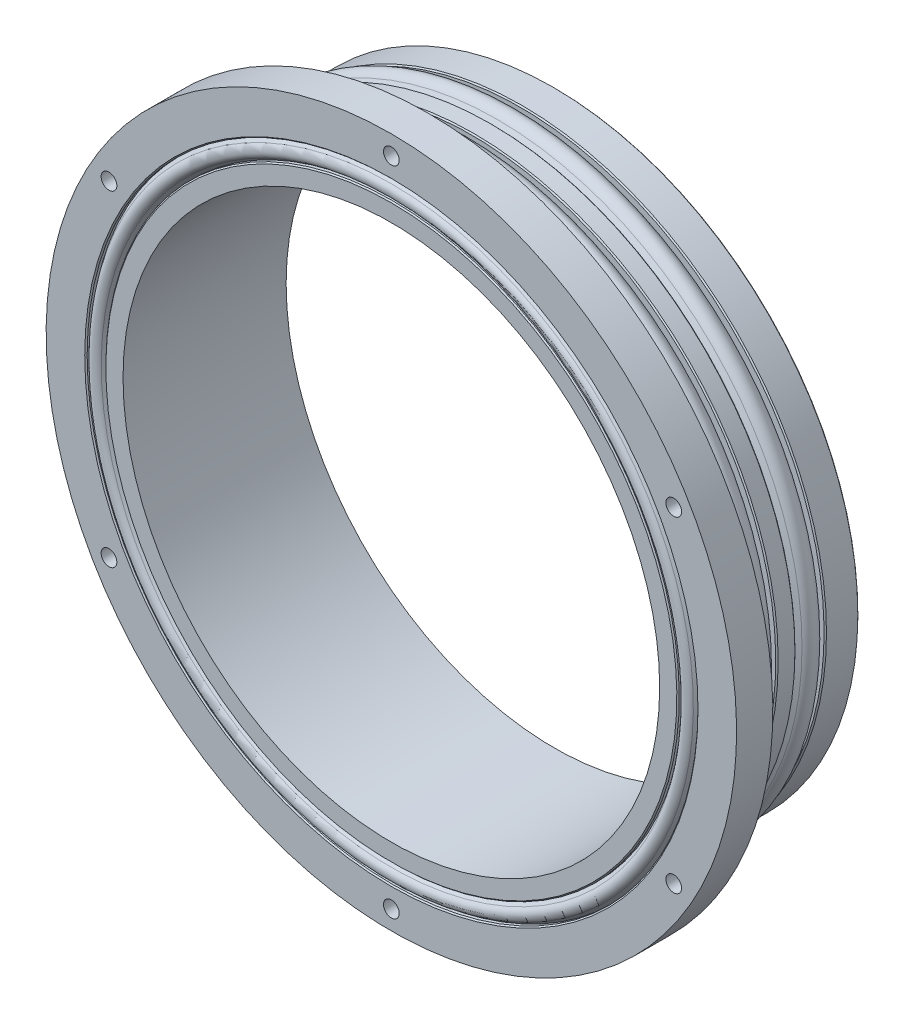
SolidWorks part; units mm, degrees
ref_plane "前视基准面" through (0, 0, 0) normal (0, 0, 1) x (1, 0, 0)
ref_plane "上视基准面" through (0, 0, 0) normal (0, 1, 0) x (1, 0, 0)
ref_plane "右视基准面" through (0, 0, 0) normal (1, 0, 0) x (0, 0, -1)
ref_plane "基准面4" through (0, 0, 0) normal (0, -1, 0) x (1, 0, 0)
sketch "草图1" plane through (0, 0, 0) normal (0, -1, 0) x (1, 0, 0)
  line L0 (47.2599, 27) -> (0, 27)
  line L1 (0, 27) -> (0, 0)
  line L2 (0, 0) -> (50.419, 0)
  line L3 (50.419, 0) -> (50.419, 5.587)
  line L4 (50.419, 5.587) -> (49.0411, 5.587)
  line L5 (49.0411, 5.587) -> (50.4317, 6.5475)
  line L6 (50.4317, 9.4525) -> (49.0411, 10.413)
  line L7 (49.0411, 10.413) -> (50.419, 10.413)
  line L8 (50.419, 10.413) -> (50.419, 13.587)
  line L9 (50.419, 13.587) -> (49.0411, 13.587)
  line L10 (49.0411, 13.587) -> (50.4317, 14.5475)
  line L11 (50.4317, 17.4525) -> (49.0411, 18.413)
  line L12 (49.0411, 18.413) -> (50.419, 18.413)
  line L13 (50.419, 18.413) -> (50.419, 21)
  line L14 (50.419, 21) -> (57.15, 21)
  line L15 (57.15, 21) -> (57.15, 27)
  line L16 (57.15, 27) -> (50.5587, 27)
  line L17 (50.5587, 27) -> (50.5587, 26.2792)
  line L18 (50.5587, 26.2792) -> (50.0138, 27.019)
  line L19 (48.0048, 27.019) -> (47.4599, 26.2792)
  line L20 (47.4599, 26.2792) -> (47.4599, 26.8)
  line L21 (47.4599, 26.8) -> (47.2599, 27)
  line L22 (0, 27.5267) -> (0, 0) construction
  arc A0 (50.4317, 6.5475) -> (50.4317, 9.4525) centre (49.4284, 8) ccw
  arc A1 (50.4317, 14.5475) -> (50.4317, 17.4525) centre (49.4284, 16) ccw
  arc A2 (50.0138, 27.019) -> (48.0048, 27.019) centre (49.0093, 26.2792) ccw
revolve "旋转1" add sketch "草图1" angle 360 about L22
hole_wizard "Ø2.6 (2.6) 直径孔1" positions "草图3" profile "草图2" hole size "Ø2.6" standard "ANSI Metric"
sketch "草图3" plane through (0, 0, 0) normal (0, 0, -1) x (-1, 0, 0)
  point P0 (-46.99, 0)
  point P1 (0, 46.99)
  point P2 (46.99, 0)
  point P3 (0, -46.99)
sketch "草图2" plane through (46.99, 0, 0) normal (1, 0, 0) x (0, 1, 0)
  line L0 (0, 0) -> (0, 4)
  line L1 (0, 4) -> (1.3, 4)
  line L2 (1.3, 4) -> (1.3, 0)
  line L5 (1.3, 0) -> (0, 0)
  line L10 (0, 4) -> (-1.3, 4) construction
  line L11 (0, -6.35) -> (0, 107.95) construction
  dimension "孔直径" = 2.6
  dimension "孔深度" = 4
  dimension "导头角度" = 180
hole_wizard "Ø2.6 (2.6) 直径孔2" positions "草图5" profile "草图4" hole size "Ø2.6" standard "ANSI Metric"
sketch "草图5" plane through (0, 0, 21) normal (0, 0, -1) x (-1, 0, 0)
  point P0 (0, 53.975)
  point P1 (-46.7437, 26.9875)
  point P2 (-46.7437, -26.9875)
  point P3 (0, -53.975)
  point P4 (46.7437, -26.9875)
  point P5 (46.7437, 26.9875)
sketch "草图4" plane through (0, 53.975, 21) normal (1, 0, 0) x (0, 1, 0)
  line L0 (0, 0) -> (0, 6.5267)
  line L1 (0, 6.5267) -> (1.3, 6.5267)
  line L2 (1.3, 6.5267) -> (1.3, 0)
  line L5 (1.3, 0) -> (0, 0)
  line L11 (0, -6.35) -> (0, 107.95) construction
  dimension "通孔孔直径" = 2.6
  dimension "通孔孔深度" = 6.5267
hole_wizard "M80 间隙孔1" positions "草图7" profile "草图6" hole size "M80" standard "ANSI Metric"
sketch "草图7" plane through (0, 0, 27) normal (0, 0, 1) x (1, 0, 0)
  point P0 (0, 0)
sketch "草图6" plane through (0, 0, 27) normal (1, 0, 0) x (0, -1, 0)
  line L0 (0, 0) -> (0, 27)
  line L1 (0, 27) -> (44.419, 27)
  line L2 (44.419, 27) -> (44.419, 0)
  line L5 (44.419, 0) -> (0, 0)
  line L11 (0, -6.35) -> (0, 107.95) construction
  dimension "通孔孔直径" = 88.838
  dimension "通孔孔深度" = 27
chamfer "倒角1" distance 0.2 angle 45 6 edges at (0, 50.419, 5.587) (0, 50.419, 13.587) (0, 50.419, 10.413) (0, 50.419, 0) (0, 50.5587, 27) (0, 50.419, 18.413)
